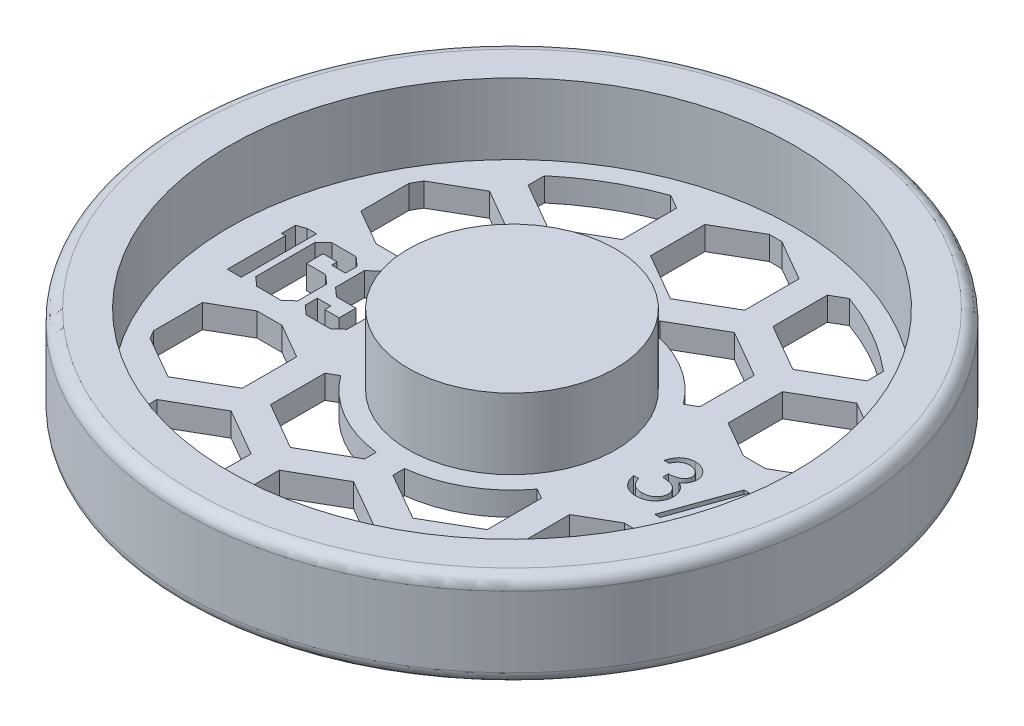
SolidWorks part; units mm, degrees
ref_plane "Front Plane" through (0, 0, 0) normal (0, 0, 1) x (1, 0, 0)
ref_plane "Top Plane" through (0, 0, 0) normal (0, 1, 0) x (1, 0, 0)
ref_plane "Right Plane" through (0, 0, 0) normal (1, 0, 0) x (0, 0, -1)
sketch "Sketch1" plane through (0, 0, 0) normal (0, 0, 1) x (1, 0, 0)
  line L0 (0, 0) -> (0, 12.7)
  line L1 (0, 12.7) -> (13.97, 12.7)
  line L2 (13.97, 12.7) -> (13.97, 3.175)
  line L3 (13.97, 3.175) -> (38.1, 3.175)
  line L4 (38.1, 3.175) -> (38.1, 12.7)
  line L5 (38.1, 12.7) -> (42.8625, 12.7)
  line L6 (44.45, 11.1125) -> (44.45, 1.5875)
  line L7 (42.8625, 0) -> (0, 0)
  arc A0 (42.8625, 0) -> (44.45, 1.5875) centre (42.8625, 1.5875) ccw
  arc A1 (44.45, 11.1125) -> (42.8625, 12.7) centre (42.8625, 11.1125) ccw
  dimension "D7" = 1.5875
  dimension "D1" = 3.175
  dimension "D2" = 6.35
  dimension "D3" = 38.1
  dimension "D4" = 13.97
  dimension "D5" = 9.525
  dimension "D6" = 9.525
revolve "Revolve1" add sketch "Sketch1" angle 360 about L0
sketch "Sketch2" plane through (0, 3.175, 0) normal (0, 1, 0) x (1, 0, 0)
  line L0 (-13.97, 0) -> (-38.1, 0) construction
  line L1 (13.97, 0) -> (38.1, 0) construction
  line L2 (-13.97, -5.08) -> (-38.1, -5.08) construction
  line L3 (13.97, -3.81) -> (38.1, -3.81) construction
  circle A0 centre (0, 0) radius 13.97 construction
  circle A1 centre (0, 0) radius 13.97 construction
  circle A2 centre (0, 0) radius 38.1 construction
  circle A3 centre (0, 0) radius 38.1 construction
  text T0 "169" font "Jersey M54" height 10.16
  text T1 "3/8\r\n" font "Century Gothic" height 7.62
  dimension "D1" = 5.08
  dimension "D2" = 3.81
extrude "Cut-Extrude1" cut sketch "Sketch2" against normal through all both and the other way through all
sketch "Sketch3" plane through (0, 3.175, 0) normal (0, 1, 0) x (1, 0, 0)
  line L0 (0, -7.9375) -> (0, 7.9375)
  line L1 (-34.6628, 7.9375) -> (34.6628, 7.9375)
  line L2 (-34.6628, -7.9375) -> (34.6628, -7.9375)
  line L3 (16.51, -7.3323) -> (22.86, -3.6662)
  line L4 (0, -7.3323) -> (6.35, -3.6662)
  line L5 (6.35, -3.6662) -> (6.35, 3.6662)
  line L6 (6.35, 3.6662) -> (0, 7.3323)
  line L7 (0, 7.3323) -> (-6.35, 3.6662)
  line L8 (-6.35, 3.6662) -> (-6.35, -3.6662)
  line L9 (-6.35, -3.6662) -> (0, -7.3323)
  line L10 (8.255, -6.9657) -> (1.905, -10.6319)
  line L11 (1.905, -10.6319) -> (1.905, -17.9643)
  line L12 (1.905, -17.9643) -> (8.255, -21.6304)
  line L13 (8.255, -21.6304) -> (14.605, -17.9643)
  line L14 (14.605, -17.9643) -> (14.605, -10.6319)
  line L15 (14.605, -10.6319) -> (8.255, -6.9657)
  line L16 (22.86, -3.6662) -> (22.86, 3.6662)
  line L17 (22.86, 3.6662) -> (16.51, 7.3323)
  line L18 (16.51, 7.3323) -> (10.16, 3.6662)
  line L19 (10.16, 3.6662) -> (10.16, -3.6662)
  line L20 (10.16, -3.6662) -> (16.51, -7.3323)
  line L21 (24.765, -6.9657) -> (18.415, -10.6319)
  line L22 (18.415, -10.6319) -> (18.415, -17.9643)
  line L23 (18.415, -17.9643) -> (24.765, -21.6304)
  line L24 (24.765, -21.6304) -> (31.115, -17.9643)
  line L25 (31.115, -17.9643) -> (31.115, -10.6319)
  line L26 (31.115, -10.6319) -> (24.765, -6.9657)
  line L27 (33.02, -7.3323) -> (39.37, -3.6662)
  line L28 (39.37, -3.6662) -> (39.37, 3.6662)
  line L29 (39.37, 3.6662) -> (33.02, 7.3323)
  line L30 (33.02, 7.3323) -> (26.67, 3.6662)
  line L31 (26.67, 3.6662) -> (26.67, -3.6662)
  line L32 (26.67, -3.6662) -> (33.02, -7.3323)
  line L33 (41.275, -6.9657) -> (34.925, -10.6319)
  line L34 (34.925, -10.6319) -> (34.925, -17.9643)
  line L35 (34.925, -17.9643) -> (41.275, -21.6304)
  line L36 (41.275, -21.6304) -> (47.625, -17.9643)
  line L37 (47.625, -17.9643) -> (47.625, -10.6319)
  line L38 (47.625, -10.6319) -> (41.275, -6.9657)
  line L39 (-16.51, -7.3323) -> (-10.16, -3.6662)
  line L40 (-10.16, -3.6662) -> (-10.16, 3.6662)
  line L41 (-10.16, 3.6662) -> (-16.51, 7.3323)
  line L42 (-16.51, 7.3323) -> (-22.86, 3.6662)
  line L43 (-22.86, 3.6662) -> (-22.86, -3.6662)
  line L44 (-22.86, -3.6662) -> (-16.51, -7.3323)
  line L45 (-8.255, -6.9657) -> (-14.605, -10.6319)
  line L46 (-14.605, -10.6319) -> (-14.605, -17.9643)
  line L47 (-14.605, -17.9643) -> (-8.255, -21.6304)
  line L48 (-8.255, -21.6304) -> (-1.905, -17.9643)
  line L49 (-1.905, -17.9643) -> (-1.905, -10.6319)
  line L50 (-1.905, -10.6319) -> (-8.255, -6.9657)
  line L51 (-33.02, -7.3323) -> (-26.67, -3.6662)
  line L52 (-26.67, -3.6662) -> (-26.67, 3.6662)
  line L53 (-26.67, 3.6662) -> (-33.02, 7.3323)
  line L54 (-33.02, 7.3323) -> (-39.37, 3.6662)
  line L55 (-39.37, 3.6662) -> (-39.37, -3.6662)
  line L56 (-39.37, -3.6662) -> (-33.02, -7.3323)
  line L57 (-24.765, -6.9657) -> (-31.115, -10.6319)
  line L58 (-31.115, -10.6319) -> (-31.115, -17.9643)
  line L59 (-31.115, -17.9643) -> (-24.765, -21.6304)
  line L60 (-24.765, -21.6304) -> (-18.415, -17.9643)
  line L61 (-18.415, -17.9643) -> (-18.415, -10.6319)
  line L62 (-18.415, -10.6319) -> (-24.765, -6.9657)
  line L63 (-49.53, -7.3323) -> (-43.18, -3.6662)
  line L64 (-43.18, -3.6662) -> (-43.18, 3.6662)
  line L65 (-43.18, 3.6662) -> (-49.53, 7.3323)
  line L66 (-49.53, 7.3323) -> (-55.88, 3.6662)
  line L67 (-55.88, 3.6662) -> (-55.88, -3.6662)
  line L68 (-55.88, -3.6662) -> (-49.53, -7.3323)
  line L69 (-41.275, -6.9657) -> (-47.625, -10.6319)
  line L70 (-47.625, -10.6319) -> (-47.625, -17.9643)
  line L71 (-47.625, -17.9643) -> (-41.275, -21.6304)
  line L72 (-41.275, -21.6304) -> (-34.925, -17.9643)
  line L73 (-34.925, -17.9643) -> (-34.925, -10.6319)
  line L74 (-34.925, -10.6319) -> (-41.275, -6.9657)
  line L75 (0, 21.3697) -> (6.35, 25.0358)
  line L76 (6.35, 25.0358) -> (6.35, 32.3682)
  line L77 (6.35, 32.3682) -> (0, 36.0343)
  line L78 (0, 36.0343) -> (-6.35, 32.3682)
  line L79 (-6.35, 32.3682) -> (-6.35, 25.0358)
  line L80 (-6.35, 25.0358) -> (0, 21.3697)
  line L81 (8.255, 21.7363) -> (1.905, 18.0701)
  line L82 (1.905, 18.0701) -> (1.905, 10.7377)
  line L83 (1.905, 10.7377) -> (8.255, 7.0716)
  line L84 (8.255, 7.0716) -> (14.605, 10.7377)
  line L85 (14.605, 10.7377) -> (14.605, 18.0701)
  line L86 (14.605, 18.0701) -> (8.255, 21.7363)
  line L87 (16.51, 21.3697) -> (22.86, 25.0358)
  line L88 (22.86, 25.0358) -> (22.86, 32.3682)
  line L89 (22.86, 32.3682) -> (16.51, 36.0343)
  line L90 (16.51, 36.0343) -> (10.16, 32.3682)
  line L91 (10.16, 32.3682) -> (10.16, 25.0358)
  line L92 (10.16, 25.0358) -> (16.51, 21.3697)
  line L93 (24.765, 21.7363) -> (18.415, 18.0701)
  line L94 (18.415, 18.0701) -> (18.415, 10.7377)
  line L95 (18.415, 10.7377) -> (24.765, 7.0716)
  line L96 (24.765, 7.0716) -> (31.115, 10.7377)
  line L97 (31.115, 10.7377) -> (31.115, 18.0701)
  line L98 (31.115, 18.0701) -> (24.765, 21.7363)
  line L99 (33.02, 21.3697) -> (39.37, 25.0358)
  line L100 (39.37, 25.0358) -> (39.37, 32.3682)
  line L101 (39.37, 32.3682) -> (33.02, 36.0343)
  line L102 (33.02, 36.0343) -> (26.67, 32.3682)
  line L103 (26.67, 32.3682) -> (26.67, 25.0358)
  line L104 (26.67, 25.0358) -> (33.02, 21.3697)
  line L105 (41.275, 21.7363) -> (34.925, 18.0701)
  line L106 (34.925, 18.0701) -> (34.925, 10.7377)
  line L107 (34.925, 10.7377) -> (41.275, 7.0716)
  line L108 (41.275, 7.0716) -> (47.625, 10.7377)
  line L109 (47.625, 10.7377) -> (47.625, 18.0701)
  line L110 (47.625, 18.0701) -> (41.275, 21.7363)
  line L111 (-16.51, 21.3697) -> (-10.16, 25.0358)
  line L112 (-10.16, 25.0358) -> (-10.16, 32.3682)
  line L113 (-10.16, 32.3682) -> (-16.51, 36.0343)
  line L114 (-16.51, 36.0343) -> (-22.86, 32.3682)
  line L115 (-22.86, 32.3682) -> (-22.86, 25.0358)
  line L116 (-22.86, 25.0358) -> (-16.51, 21.3697)
  line L117 (-8.255, 21.7363) -> (-14.605, 18.0701)
  line L118 (-14.605, 18.0701) -> (-14.605, 10.7377)
  line L119 (-14.605, 10.7377) -> (-8.255, 7.0716)
  line L120 (-8.255, 7.0716) -> (-1.905, 10.7377)
  line L121 (-1.905, 10.7377) -> (-1.905, 18.0701)
  line L122 (-1.905, 18.0701) -> (-8.255, 21.7363)
  line L123 (-24.765, 21.7363) -> (-31.115, 18.0701)
  line L124 (-31.115, 18.0701) -> (-31.115, 10.7377)
  line L125 (-31.115, 10.7377) -> (-24.765, 7.0716)
  line L126 (-24.765, 7.0716) -> (-18.415, 10.7377)
  line L127 (-18.415, 10.7377) -> (-18.415, 18.0701)
  line L128 (-18.415, 18.0701) -> (-24.765, 21.7363)
  line L129 (-33.02, 21.3697) -> (-26.67, 25.0358)
  line L130 (-26.67, 25.0358) -> (-26.67, 32.3682)
  line L131 (-26.67, 32.3682) -> (-33.02, 36.0343)
  line L132 (-33.02, 36.0343) -> (-39.37, 32.3682)
  line L133 (-39.37, 32.3682) -> (-39.37, 25.0358)
  line L134 (-39.37, 25.0358) -> (-33.02, 21.3697)
  line L135 (-49.53, 21.3697) -> (-43.18, 25.0358)
  line L136 (-43.18, 25.0358) -> (-43.18, 32.3682)
  line L137 (-43.18, 32.3682) -> (-49.53, 36.0343)
  line L138 (-49.53, 36.0343) -> (-55.88, 32.3682)
  line L139 (-55.88, 32.3682) -> (-55.88, 25.0358)
  line L140 (-55.88, 25.0358) -> (-49.53, 21.3697)
  line L141 (-41.275, 21.7363) -> (-47.625, 18.0701)
  line L142 (-47.625, 18.0701) -> (-47.625, 10.7377)
  line L143 (-47.625, 10.7377) -> (-41.275, 7.0716)
  line L144 (-41.275, 7.0716) -> (-34.925, 10.7377)
  line L145 (-34.925, 10.7377) -> (-34.925, 18.0701)
  line L146 (-34.925, 18.0701) -> (-41.275, 21.7363)
  line L147 (0, -36.0343) -> (6.35, -32.3682)
  line L148 (6.35, -32.3682) -> (6.35, -25.0358)
  line L149 (6.35, -25.0358) -> (0, -21.3697)
  line L150 (0, -21.3697) -> (-6.35, -25.0358)
  line L151 (-6.35, -25.0358) -> (-6.35, -32.3682)
  line L152 (-6.35, -32.3682) -> (0, -36.0343)
  line L153 (8.255, -35.6677) -> (1.905, -39.3339)
  line L154 (1.905, -39.3339) -> (1.905, -46.6663)
  line L155 (1.905, -46.6663) -> (8.255, -50.3324)
  line L156 (8.255, -50.3324) -> (14.605, -46.6663)
  line L157 (14.605, -46.6663) -> (14.605, -39.3339)
  line L158 (14.605, -39.3339) -> (8.255, -35.6677)
  line L159 (16.51, -36.0343) -> (22.86, -32.3682)
  line L160 (22.86, -32.3682) -> (22.86, -25.0358)
  line L161 (22.86, -25.0358) -> (16.51, -21.3697)
  line L162 (16.51, -21.3697) -> (10.16, -25.0358)
  line L163 (10.16, -25.0358) -> (10.16, -32.3682)
  line L164 (10.16, -32.3682) -> (16.51, -36.0343)
  line L165 (24.765, -35.6677) -> (18.415, -39.3339)
  line L166 (18.415, -39.3339) -> (18.415, -46.6663)
  line L167 (18.415, -46.6663) -> (24.765, -50.3324)
  line L168 (24.765, -50.3324) -> (31.115, -46.6663)
  line L169 (31.115, -46.6663) -> (31.115, -39.3339)
  line L170 (31.115, -39.3339) -> (24.765, -35.6677)
  line L171 (33.02, -36.0343) -> (39.37, -32.3682)
  line L172 (39.37, -32.3682) -> (39.37, -25.0358)
  line L173 (39.37, -25.0358) -> (33.02, -21.3697)
  line L174 (33.02, -21.3697) -> (26.67, -25.0358)
  line L175 (26.67, -25.0358) -> (26.67, -32.3682)
  line L176 (26.67, -32.3682) -> (33.02, -36.0343)
  line L177 (41.275, -35.6677) -> (34.925, -39.3339)
  line L178 (34.925, -39.3339) -> (34.925, -46.6663)
  line L179 (34.925, -46.6663) -> (41.275, -50.3324)
  line L180 (41.275, -50.3324) -> (47.625, -46.6663)
  line L181 (47.625, -46.6663) -> (47.625, -39.3339)
  line L182 (47.625, -39.3339) -> (41.275, -35.6677)
  line L183 (-16.51, -36.0343) -> (-10.16, -32.3682)
  line L184 (-10.16, -32.3682) -> (-10.16, -25.0358)
  line L185 (-10.16, -25.0358) -> (-16.51, -21.3697)
  line L186 (-16.51, -21.3697) -> (-22.86, -25.0358)
  line L187 (-22.86, -25.0358) -> (-22.86, -32.3682)
  line L188 (-22.86, -32.3682) -> (-16.51, -36.0343)
  line L189 (-8.255, -35.6677) -> (-14.605, -39.3339)
  line L190 (-14.605, -39.3339) -> (-14.605, -46.6663)
  line L191 (-14.605, -46.6663) -> (-8.255, -50.3324)
  line L192 (-8.255, -50.3324) -> (-1.905, -46.6663)
  line L193 (-1.905, -46.6663) -> (-1.905, -39.3339)
  line L194 (-1.905, -39.3339) -> (-8.255, -35.6677)
  line L195 (-24.765, -35.6677) -> (-31.115, -39.3339)
  line L196 (-31.115, -39.3339) -> (-31.115, -46.6663)
  line L197 (-31.115, -46.6663) -> (-24.765, -50.3324)
  line L198 (-24.765, -50.3324) -> (-18.415, -46.6663)
  line L199 (-18.415, -46.6663) -> (-18.415, -39.3339)
  line L200 (-18.415, -39.3339) -> (-24.765, -35.6677)
  line L201 (-33.02, -36.0343) -> (-26.67, -32.3682)
  line L202 (-26.67, -32.3682) -> (-26.67, -25.0358)
  line L203 (-26.67, -25.0358) -> (-33.02, -21.3697)
  line L204 (-33.02, -21.3697) -> (-39.37, -25.0358)
  line L205 (-39.37, -25.0358) -> (-39.37, -32.3682)
  line L206 (-39.37, -32.3682) -> (-33.02, -36.0343)
  line L207 (-49.53, -36.0343) -> (-43.18, -32.3682)
  line L208 (-43.18, -32.3682) -> (-43.18, -25.0358)
  line L209 (-43.18, -25.0358) -> (-49.53, -21.3697)
  line L210 (-49.53, -21.3697) -> (-55.88, -25.0358)
  line L211 (-55.88, -25.0358) -> (-55.88, -32.3682)
  line L212 (-55.88, -32.3682) -> (-49.53, -36.0343)
  line L213 (-41.275, -35.6677) -> (-47.625, -39.3339)
  line L214 (-47.625, -39.3339) -> (-47.625, -46.6663)
  line L215 (-47.625, -46.6663) -> (-41.275, -50.3324)
  line L216 (-41.275, -50.3324) -> (-34.925, -46.6663)
  line L217 (-34.925, -46.6663) -> (-34.925, -39.3339)
  line L218 (-34.925, -39.3339) -> (-41.275, -35.6677)
  circle A0 centre (0, 0) radius 35.56
  circle A1 centre (0, 0) radius 16.51
  circle A2 centre (0, 0) radius 6.35 construction
  circle A3 centre (8.255, -14.2981) radius 6.35 construction
  point P7 (0, 0)
  point P10 (0, 7.9375)
  point P13 (0, -7.9375)
  dimension "D1" = 71.12
  dimension "D2" = 33.02
  dimension "D3" = 15.875
  dimension "D4" = 12.7
  dimension "D5" = 12.7
  dimension "D6" = 3.81
  dimension "D7" = 1.905
  dimension "D8" = 3
  dimension "D9" = 4
  dimension "D10" = 2
  dimension "D11" = 2
extrude "Cut-Extrude4" cut sketch "Sketch3" against normal through all both and the other way through all contours L113 A0 L115 L116 L111 L112 | L123 A0 L124 L125 L1 L126 L127 L128 | A1 L121 L122 L117 L118 L119 | L77 A0 L78 L79 L80 L75 L76 | L88 A0 L90 L91 L92 L87 | A1 L84 L85 L86 L81 L82 | L97 A0 L98 L93 L94 L95 L1 L96 | L24 A0 L25 L26 L2 L21 L22 L23 | A1 L11 L12 L13 L14 L15 | L164 A0 L160 L161 L162 L163 | L152 A0 L147 L148 L149 L150 L151 | A1 L45 L46 L47 L48 L49 | L187 A0 L183 L184 L185 L186 | L58 A0 L59 L60 L61 L62 L2 L57
